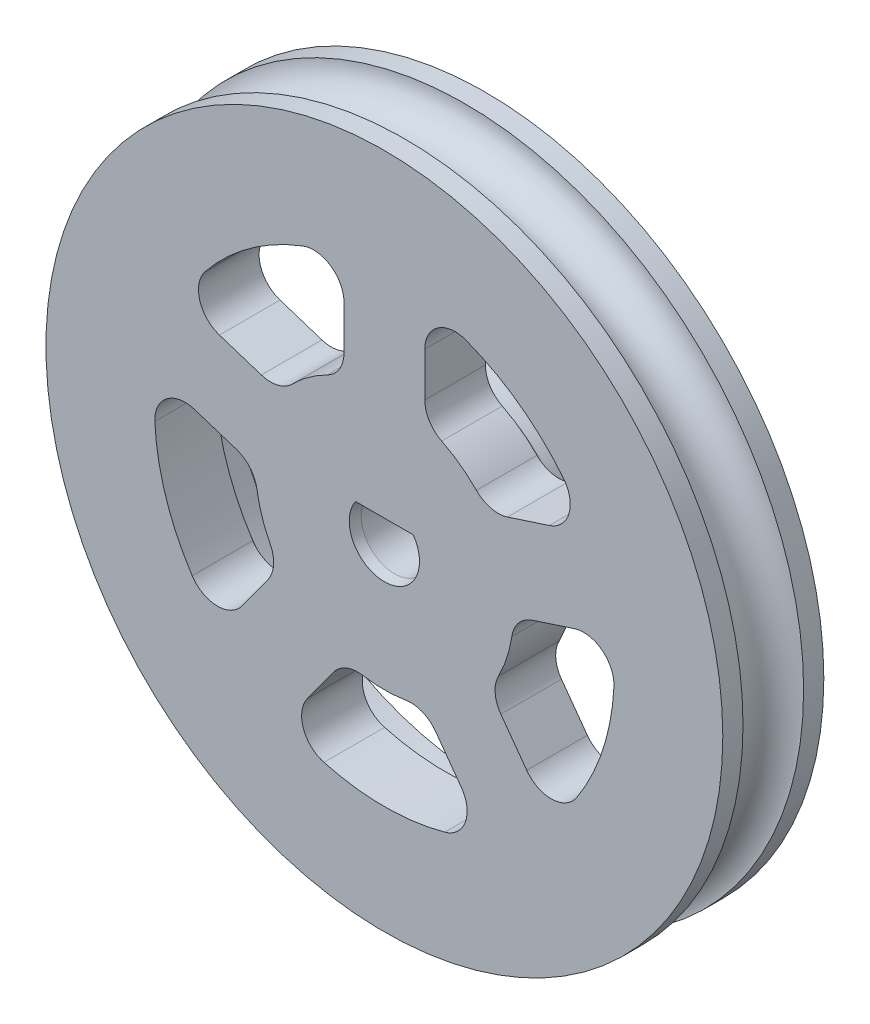
SolidWorks part; units mm, degrees
ref_plane "Front Plane" through (0, 0, 0) normal (0, 0, 1) x (1, 0, 0)
ref_plane "Top Plane" through (0, 0, 0) normal (0, 1, 0) x (1, 0, 0)
ref_plane "Right Plane" through (0, 0, 0) normal (1, 0, 0) x (0, 0, -1)
sketch "Sketch3" plane through (0, 0, 0) normal (0, 1, 0) x (1, 0, 0)
  line L14 (0, -2.5) -> (-16.75, -2.5)
  line L15 (-16.75, -2.5) -> (-16.75, -1.5)
  line L16 (-16.75, 1.5) -> (-16.75, 2.5)
  line L17 (-16.75, 2.5) -> (0, 2.5)
  line L19 (0, -2.5) -> (0, 2.5)
  line L20 (0, 7.5) -> (0, -7.5) construction
  arc A1 (-16.75, -1.5) -> (-16.75, 1.5) centre (-16.75, 0) ccw
  point P1 (0, 0)
  point P4 (0, 0)
  point P12 (0, 0)
  point P13 (-15.25, 0)
  dimension "D1" = 1.5
  dimension "D2" = 5
  dimension "D3" = 30.5
revolve "Revolve1" add sketch "Sketch3" angle 360 about L19
sketch "Sketch7" plane through (0, 0, -2.5) normal (0, 0, 1) x (1, 0, 0)
  circle A0 centre (0, 0) radius 12.75
  circle A2 centre (0, 0) radius 16.75 construction
  dimension "D1" = 4
extrude "Cut-Extrude3" cut sketch "Sketch7" along normal blind 2
sketch "Sketch8" plane through (0, 0, -0.5) normal (0, 0, 1) x (1, 0, 0)
  arc A2 (-1.118, 1) -> (1.118, 1) centre (0, 0) ccw construction
  circle A5 centre (0, 0) radius 5
  dimension "D1" = 10
extrude "Boss-Extrude1" add sketch "Sketch8" against normal blind 5
sketch "Sketch6" plane through (0, 0, -5.5) normal (0, 0, 1) x (1, 0, 0)
  line L0 (-1.3829, 0.9) -> (1.3829, 0.9)
  arc A0 (-1.3829, 0.9) -> (1.3829, 0.9) centre (0, 0) ccw
  point P5 (0, -1.65)
  dimension "D1" = 3.3
  dimension "D2" = 2.55
extrude "Cut-Extrude4" cut sketch "Sketch6" along normal through all contours A0 L0
fillet "Fillet1" radius 1 2 edges at (5, 0, -0.5) (12.75, 0, -0.5)
chamfer "Chamfer1" distance 0.5 angle 10 2 edges at (0, 0.9, -5.5) (0, -1.65, -5.5)
chamfer "Chamfer2" distance 0.5 angle 10 2 edges at (0, 0.9, 2.5) (0, -1.65, 2.5)
sketch "Sketch11" plane through (0, 0, -0.5) normal (0, 0, -1) x (-1, 0, 0)
  line L0 (-12.75, 0) -> (-11.375, 0) construction
  line L1 (-11.375, 0) -> (-8.875, 0) construction
  line L2 (-8.875, 0) -> (-6.375, 0) construction
  line L3 (-6.375, 0) -> (-5, 0) construction
  line L22 (-2, 11.1978) -> (-2, 6.0532)
  line L23 (2, 6.0532) -> (2, 11.1978)
  line L24 (-2, 6.0532) -> (2, 6.0532) construction
  line L25 (-2, 11.1978) -> (2, 11.1978) construction
  line L26 (0, 11.1978) -> (0, 6.0532) construction
  line L27 (6.3749, -0.0316) -> (11.2678, 1.5582)
  line L28 (10.0317, 5.3624) -> (5.1389, 3.7726)
  line L29 (1.9399, -6.0727) -> (4.9639, -10.2348)
  line L30 (8.1999, -7.8836) -> (5.176, -3.7215)
  line L31 (-5.176, -3.7215) -> (-8.1999, -7.8836)
  line L32 (-4.9639, -10.2348) -> (-1.9399, -6.0727)
  line L33 (-5.1389, 3.7726) -> (-10.0317, 5.3624)
  line L34 (-11.2678, 1.5582) -> (-6.3749, -0.0316)
  circle A0 centre (0, 0) radius 8.875 construction
  circle A1 centre (0, 0) radius 12.75 construction
  circle A3 centre (0, 0) radius 11.375
  circle A4 centre (0, 0) radius 6.375
  circle A5 centre (0, 0) radius 5 construction
  point P40 (0, 0)
  point P41 (0, 0)
  point P49 (0, 0)
  point P57 (0, 0)
  dimension "D1" = 5
  dimension "D2" = 4
  dimension "D3" = 5
extrude "Cut-Extrude7" cut sketch "Sketch11" against normal through all contours A4 L22 A3 L33 | A4 L28 A3 L23 | A4 L34 A3 L31 | A4 L30 A3 L27 | A4 L32 A3 L29
fillet "Fillet3" radius 1.5 20 edges at (4.9639, -10.2348, 1) (-4.9639, -10.2348, 1) (1.9399, -6.0727, 1) (-1.9399, -6.0727, 1) (8.1999, -7.8836, 1) (11.2678, 1.5582, 1) (-8.1999, -7.8836, 1) (5.176, -3.7215, 1) (6.3749, -0.0316, 1) (-11.2678, 1.5582, 1) (-5.176, -3.7215, 1) (-6.3749, -0.0316, 1) (10.0317, 5.3624, 1) (5.1389, 3.7726, 1) (-5.1389, 3.7726, 1) (-10.0317, 5.3624, 1) (2, 6.0532, 1) (-2, 6.0532, 1) (-2, 11.1978, 1) (2, 11.1978, 1)
sketch "Sketch10" plane through (0, 0, -0.5) normal (0, 0, -1) x (-1, 0, 0)
  line L0 (-12.75, 0) -> (-5, 0) construction
  circle A6 centre (0, 0) radius 8.875 construction
  circle A11 centre (0, 0) radius 5 construction
  circle A12 centre (0, 0) radius 5 construction
  circle A13 centre (0, 0) radius 12.75 construction
  circle A14 centre (0, 0) radius 12.75 construction
  circle A15 centre (0, 8.875) radius 2.5
  circle A16 centre (8.4406, 2.7425) radius 2.5
  circle A17 centre (5.2166, -7.18) radius 2.5
  circle A18 centre (-5.2166, -7.18) radius 2.5
  circle A19 centre (-8.4406, 2.7425) radius 2.5
  point P3 (-5, 0)
  point P4 (-12.75, 0)
  point P17 (-8.875, 0)
  point P30 (0, 0)
  dimension "D1" = 5
  dimension "D2" = 5
